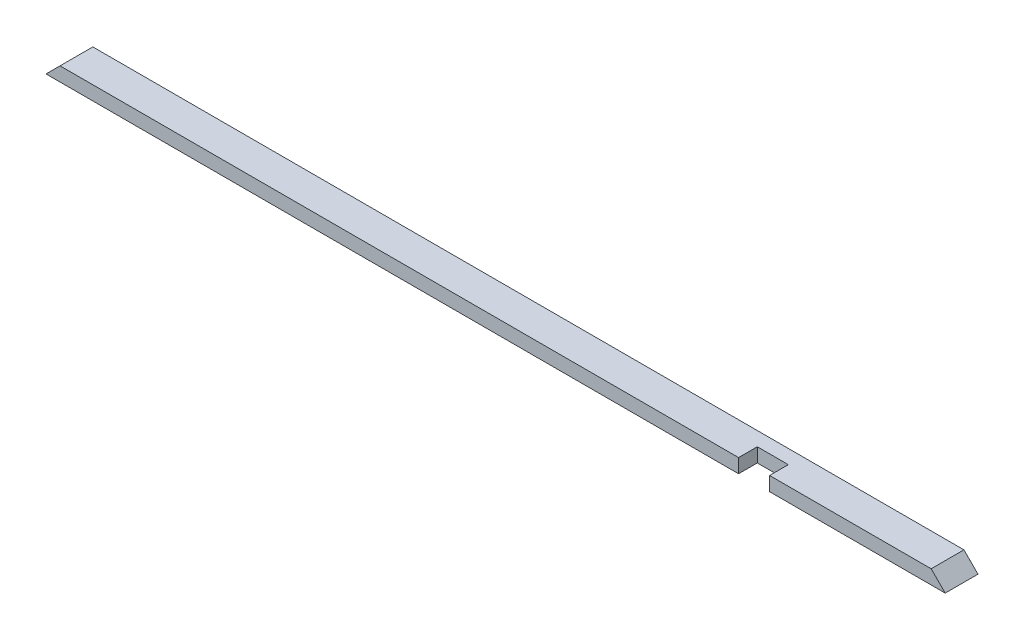
SolidWorks part; units mm, degrees
ref_plane "Front Plane" through (0, 0, 0) normal (0, 0, 1) x (1, 0, 0)
ref_plane "Top Plane" through (0, 0, 0) normal (0, 1, 0) x (1, 0, 0)
ref_plane "Right Plane" through (0, 0, 0) normal (1, 0, 0) x (0, 0, -1)
sketch "Sketch1" plane through (0, 0, 0) normal (0, 1, 0) x (1, 0, 0)
  line L1 (0, 0) -> (2438.4, 0)
  line L2 (0, 0) -> (0, 88.9)
  line L3 (0, 88.9) -> (2438.4, 88.9)
  line L4 (2438.4, 0) -> (2438.4, 88.9)
  dimension "D1" = 88.9
  dimension "D2" = 2438.4
extrude "Boss-Extrude1" add sketch "Sketch1" along normal blind 38.1
sketch "Sketch2" plane through (0, 0, 0) normal (0, 0, 1) x (1, 0, 0)
  line L0 (0, 0) -> (38.1, 38.1)
  line L1 (0, 38.1) -> (2438.4, 38.1) construction
  line L2 (38.1, 38.1) -> (0, 38.1)
  line L3 (0, 38.1) -> (0, 0)
  line L5 (2438.4, 0) -> (2438.4, 38.1)
  line L9 (2438.4, 38.1) -> (2400.3, 38.1)
  line L10 (2400.3, 38.1) -> (2438.4, 0)
  dimension "D1" = 38.1
  dimension "D2" = 38.1
  dimension "D3" = 38.1
extrude "Cut-Extrude1" cut sketch "Sketch2" against normal through all
sketch "Sketch3" plane through (0, 38.1, 0) normal (0, 1, 0) x (1, 0, 0)
  line L0 (38.1, 0) -> (2400.3, 0) construction
  line L1 (1962.15, 0) -> (1878.0125, 0)
  line L2 (1962.15, 0) -> (1962.15, 50.8)
  line L3 (1962.15, 50.8) -> (1878.0125, 50.8)
  line L4 (1878.0125, 0) -> (1878.0125, 50.8)
  point P6 (1878.0125, 25.4)
  dimension "D1" = 1878.0125
  dimension "D2" = 84.1375
  dimension "D3" = 50.8
extrude "Cut-Extrude2" cut sketch "Sketch3" against normal through all
